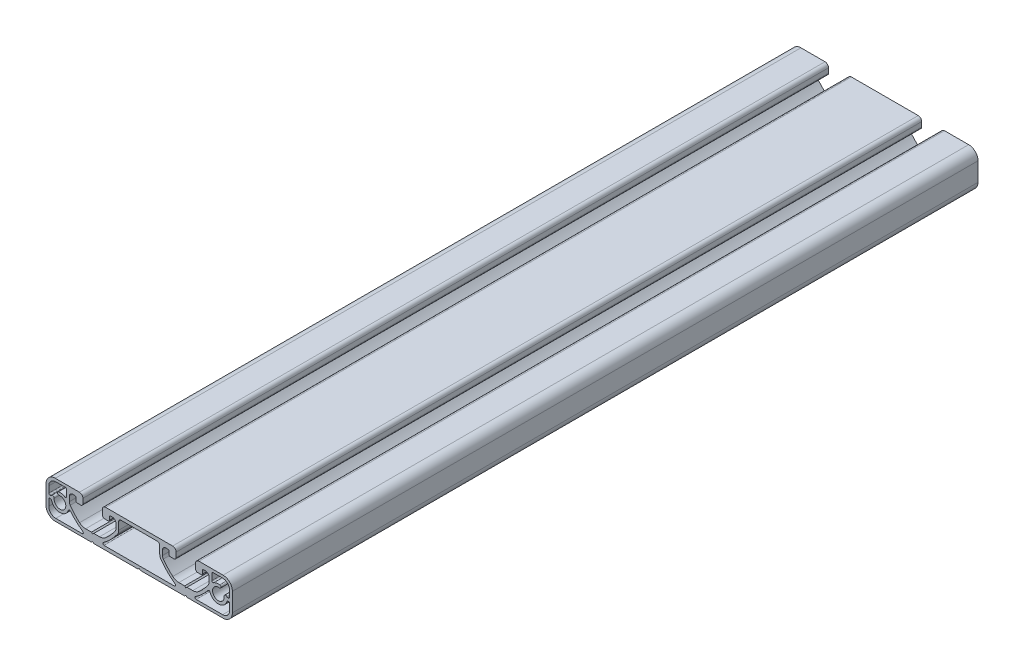
SolidWorks part; units mm, degrees
material "6063-T5"
ref_plane "Front Plane" through (0, 0, 0) normal (0, 0, 1) x (1, 0, 0)
ref_plane "Top Plane" through (0, 0, 0) normal (0, 1, 0) x (1, 0, 0)
ref_plane "Right Plane" through (0, 0, 0) normal (1, 0, 0) x (0, 0, -1)
sketch "Sketch" plane through (0, 0, 0) normal (0, 0, 1) x (1, 0, 0)
  line L0 (0, 6.5) -> (0, -6.5) construction
  line L1 (24.1507, 4.4997) -> (24.1507, 6.5)
  line L2 (26.6497, 3.4997) -> (25.1507, 3.4997)
  line L3 (27.1497, 5.3166) -> (27.1497, 3.9997)
  line L4 (28.4997, 5.8166) -> (27.6497, 5.8166)
  line L5 (29.9997, 2.3074) -> (29.9997, 4.3166)
  line L6 (20.5, -4.25) -> (22.9784, -4.25)
  line L7 (15.1167, -6.5) -> (-15.1167, -6.5)
  line L8 (-8.8007, 2.3067) -> (-8.8007, 5.5)
  line L9 (-7.8007, 6.5) -> (7.8007, 6.5)
  line L10 (20, -4.75) -> (20.5, -4.25)
  line L11 (-38.2985, -0.6) -> (-38.1037, -0.6)
  line L12 (-24.4575, -6.8) -> (-35.7985, -6.8)
  line L13 (-38.7985, -3.8) -> (-38.7985, -1.1)
  line L14 (-38.0146, 0.6) -> (-38.2985, 0.6)
  line L15 (-38.7985, 1.1) -> (-38.7985, 3.8)
  line L16 (-35.7985, 6.8) -> (-31.6985, 6.8)
  line L17 (-31.1985, 6.3) -> (-31.1985, 3.5739)
  line L18 (-25.6507, 8) -> (-36, 8)
  line L19 (-40, 4) -> (-40, -4)
  line L20 (-36, -8) -> (-20.5007, -8)
  line L21 (-20.5007, -8) -> (-20.0007, -7.5)
  line L22 (-20.0007, -7.5) -> (-19.5007, -8)
  line L23 (-19.5007, -8) -> (-0.5015, -8)
  line L24 (-0.5015, -8) -> (-0.0015, -7.5)
  line L25 (-0.0015, -7.5) -> (0.4985, -8)
  line L26 (0.4985, -8) -> (19.5007, -8)
  line L27 (19.5, -4.25) -> (20, -4.75)
  line L28 (17.0216, -4.25) -> (19.5, -4.25)
  line L29 (10, 4.3169) -> (10, 2.3077)
  line L30 (12.35, 5.8169) -> (11.5, 5.8169)
  line L31 (12.85, 4) -> (12.85, 5.3169)
  line L32 (14.8493, 3.5) -> (13.35, 3.5)
  line L33 (15.8493, 6.5) -> (15.8493, 4.5)
  line L34 (20.0007, -7.5) -> (19.5007, -8)
  line L35 (20.5007, -8) -> (20.0007, -7.5)
  line L36 (36, -8) -> (20.5007, -8)
  line L37 (40, 4) -> (40, -4)
  line L38 (25.6507, 8) -> (36, 8)
  line L39 (31.1985, 6.3) -> (31.1985, 3.5739)
  line L40 (35.7985, 6.8) -> (31.6985, 6.8)
  line L41 (38.7985, 1.1) -> (38.7985, 3.8)
  line L42 (38.0146, 0.6) -> (38.2985, 0.6)
  line L43 (38.7985, -3.8) -> (38.7985, -1.1)
  line L44 (24.4575, -6.8) -> (35.7985, -6.8)
  line L45 (38.2985, -0.6) -> (38.1037, -0.6)
  line L46 (14.3493, 8) -> (-14.3493, 8)
  line L47 (-15.8493, 6.5) -> (-15.8493, 4.5)
  line L48 (-14.8493, 3.5) -> (-13.35, 3.5)
  line L49 (-12.85, 4) -> (-12.85, 5.3169)
  line L50 (-12.35, 5.8169) -> (-11.5, 5.8169)
  line L51 (-10, 4.3169) -> (-10, 2.3077)
  line L52 (-17.0216, -4.25) -> (-19.5, -4.25)
  line L53 (-19.5, -4.25) -> (-20, -4.75)
  line L54 (-20, -4.75) -> (-20.5, -4.25)
  line L55 (-20.5, -4.25) -> (-22.9784, -4.25)
  line L56 (-29.9997, 2.3074) -> (-29.9997, 4.3166)
  line L57 (-28.4997, 5.8166) -> (-27.6497, 5.8166)
  line L58 (-27.1497, 5.3166) -> (-27.1497, 3.9997)
  line L59 (-26.6497, 3.4997) -> (-25.1507, 3.4997)
  line L60 (-24.1507, 4.4997) -> (-24.1507, 6.5)
  line L61 (8.8007, 2.3067) -> (8.8007, 5.5)
  line L62 (-24.1507, 6.5) -> (-15.8493, 6.5) construction
  line L63 (-20, -4.75) -> (-20, 6.5) construction
  arc A0 (24.1507, 6.5) -> (25.6507, 8) centre (25.6507, 6.5) cw
  arc A1 (25.1507, 3.4997) -> (24.1507, 4.4997) centre (25.1507, 4.4997) cw
  arc A2 (27.1497, 3.9997) -> (26.6497, 3.4997) centre (26.6497, 3.9997) cw
  arc A3 (27.6497, 5.8166) -> (27.1497, 5.3166) centre (27.6497, 5.3166) ccw
  arc A4 (29.9997, 4.3166) -> (28.4997, 5.8166) centre (28.4997, 4.3166) ccw
  arc A5 (29.628, 1.1462) -> (29.9997, 2.3074) centre (27.9997, 2.3074) ccw
  arc A6 (25.5888, -3.2808) -> (29.628, 1.1462) centre (9.2732, 15.6619) ccw
  arc A7 (22.9784, -4.25) -> (25.5888, -3.2808) centre (22.9784, -0.25) ccw
  arc A8 (14.4113, -3.2808) -> (17.0216, -4.25) centre (17.0216, -0.25) ccw
  arc A9 (10.3716, 1.1465) -> (14.4113, -3.2808) centre (30.726, 15.6619) ccw
  arc A10 (10, 2.3077) -> (10.3716, 1.1465) centre (12, 2.3077) ccw
  arc A11 (11.5, 5.8169) -> (10, 4.3169) centre (11.5, 4.3169) ccw
  arc A12 (12.85, 5.3169) -> (12.35, 5.8169) centre (12.35, 5.3169) ccw
  arc A13 (13.35, 3.5) -> (12.85, 4) centre (13.35, 4) cw
  arc A14 (15.8493, 4.5) -> (14.8493, 3.5) centre (14.8493, 4.5) cw
  arc A15 (14.3493, 8) -> (15.8493, 6.5) centre (14.3493, 6.5) cw
  arc A16 (40, -4) -> (36, -8) centre (36, -4) cw
  arc A17 (36, 8) -> (40, 4) centre (36, 4) cw
  arc A18 (34.5504, 3.7092) -> (34.3664, 2.4728) centre (34.4584, 3.091) cw
  arc A19 (-15.1167, -6.5) -> (-15.409, -5.5943) centre (-15.1167, -6) cw
  arc A20 (-15.409, -5.5943) -> (-9.3955, 0.4485) centre (-30.726, 15.6619) ccw
  arc A21 (-9.3955, 0.4485) -> (-8.8007, 2.3067) centre (-12.0007, 2.3067) ccw
  arc A22 (-8.8007, 5.5) -> (-7.8007, 6.5) centre (-7.8007, 5.5) cw
  arc A23 (31.9691, 3.1534) -> (34.5504, 3.7092) centre (33.9985, 0) cw
  arc A24 (-38.7985, -1.1) -> (-38.2985, -0.6) centre (-38.2985, -1.1) cw
  arc A25 (-38.1037, -0.6) -> (-37.6207, -0.9706) centre (-38.1037, -1.1) cw
  arc A26 (-37.6207, -0.9706) -> (-30.4138, -1.1011) centre (-33.9985, 0) ccw
  arc A27 (-30.4138, -1.1011) -> (-29.5489, -0.9313) centre (-29.9359, -1.248) cw
  arc A28 (-29.5489, -0.9313) -> (-24.1732, -5.8887) centre (-9.2732, 15.6619) ccw
  arc A29 (-24.1732, -5.8887) -> (-24.4575, -6.8) centre (-24.4575, -6.3) cw
  arc A30 (-35.7985, -6.8) -> (-38.7985, -3.8) centre (-35.7985, -3.8) cw
  arc A31 (-34.3664, 2.4728) -> (-36.4713, 0.3679) centre (-33.9985, 0) cw
  arc A32 (-36.4713, 0.3679) -> (-37.6035, 0.8155) centre (-37.0895, 0.4599) ccw
  arc A33 (-37.6035, 0.8155) -> (-38.0146, 0.6) centre (-38.0146, 1.1) cw
  arc A34 (-38.2985, 0.6) -> (-38.7985, 1.1) centre (-38.2985, 1.1) cw
  arc A35 (-38.7985, 3.8) -> (-35.7985, 6.8) centre (-35.7985, 3.8) cw
  arc A36 (-31.6985, 6.8) -> (-31.1985, 6.3) centre (-31.6985, 6.3) cw
  arc A37 (-31.1985, 3.5739) -> (-31.9691, 3.1534) centre (-31.6985, 3.5739) cw
  arc A38 (-31.9691, 3.1534) -> (-34.5504, 3.7092) centre (-33.9985, 0) ccw
  arc A39 (-34.5504, 3.7092) -> (-34.3664, 2.4728) centre (-34.4584, 3.091) ccw
  arc A40 (-36, 8) -> (-40, 4) centre (-36, 4) ccw
  arc A41 (-40, -4) -> (-36, -8) centre (-36, -4) ccw
  arc A42 (31.1985, 3.5739) -> (31.9691, 3.1534) centre (31.6985, 3.5739) ccw
  arc A43 (31.6985, 6.8) -> (31.1985, 6.3) centre (31.6985, 6.3) ccw
  arc A44 (38.7985, 3.8) -> (35.7985, 6.8) centre (35.7985, 3.8) ccw
  arc A45 (38.2985, 0.6) -> (38.7985, 1.1) centre (38.2985, 1.1) ccw
  arc A46 (37.6035, 0.8155) -> (38.0146, 0.6) centre (38.0146, 1.1) ccw
  arc A47 (36.4713, 0.3679) -> (37.6035, 0.8155) centre (37.0895, 0.4599) cw
  arc A48 (34.3664, 2.4728) -> (36.4713, 0.3679) centre (33.9985, 0) ccw
  arc A49 (35.7985, -6.8) -> (38.7985, -3.8) centre (35.7985, -3.8) ccw
  arc A50 (24.1732, -5.8887) -> (24.4575, -6.8) centre (24.4575, -6.3) ccw
  arc A51 (29.5489, -0.9313) -> (24.1732, -5.8887) centre (9.2732, 15.6619) cw
  arc A52 (30.4138, -1.1011) -> (29.5489, -0.9313) centre (29.9359, -1.248) ccw
  arc A53 (37.6207, -0.9706) -> (30.4138, -1.1011) centre (33.9985, 0) cw
  arc A54 (38.1037, -0.6) -> (37.6207, -0.9706) centre (38.1037, -1.1) ccw
  arc A55 (38.7985, -1.1) -> (38.2985, -0.6) centre (38.2985, -1.1) ccw
  arc A56 (8.8007, 5.5) -> (7.8007, 6.5) centre (7.8007, 5.5) ccw
  arc A57 (9.3955, 0.4485) -> (8.8007, 2.3067) centre (12.0007, 2.3067) cw
  arc A58 (15.409, -5.5943) -> (9.3955, 0.4485) centre (30.726, 15.6619) cw
  arc A59 (15.1167, -6.5) -> (15.409, -5.5943) centre (15.1167, -6) ccw
  arc A60 (-14.3493, 8) -> (-15.8493, 6.5) centre (-14.3493, 6.5) ccw
  arc A61 (-15.8493, 4.5) -> (-14.8493, 3.5) centre (-14.8493, 4.5) ccw
  arc A62 (-13.35, 3.5) -> (-12.85, 4) centre (-13.35, 4) ccw
  arc A63 (-12.85, 5.3169) -> (-12.35, 5.8169) centre (-12.35, 5.3169) cw
  arc A64 (-11.5, 5.8169) -> (-10, 4.3169) centre (-11.5, 4.3169) cw
  arc A65 (-10, 2.3077) -> (-10.3716, 1.1465) centre (-12, 2.3077) cw
  arc A66 (-10.3716, 1.1465) -> (-14.4113, -3.2808) centre (-30.726, 15.6619) cw
  arc A67 (-14.4113, -3.2808) -> (-17.0216, -4.25) centre (-17.0216, -0.25) cw
  arc A68 (-22.9784, -4.25) -> (-25.5888, -3.2808) centre (-22.9784, -0.25) cw
  arc A69 (-25.5888, -3.2808) -> (-29.628, 1.1462) centre (-9.2732, 15.6619) cw
  arc A70 (-29.628, 1.1462) -> (-29.9997, 2.3074) centre (-27.9997, 2.3074) cw
  arc A71 (-29.9997, 4.3166) -> (-28.4997, 5.8166) centre (-28.4997, 4.3166) cw
  arc A72 (-27.6497, 5.8166) -> (-27.1497, 5.3166) centre (-27.6497, 5.3166) cw
  arc A73 (-27.1497, 3.9997) -> (-26.6497, 3.4997) centre (-26.6497, 3.9997) ccw
  arc A74 (-25.1507, 3.4997) -> (-24.1507, 4.4997) centre (-25.1507, 4.4997) ccw
  arc A75 (-24.1507, 6.5) -> (-25.6507, 8) centre (-25.6507, 6.5) ccw
  dimension "D1" = 40
  dimension "D2" = 80
  dimension "D3" = 16
extrude "Boss-Extrude2" add sketch "Sketch" along normal blind 320
